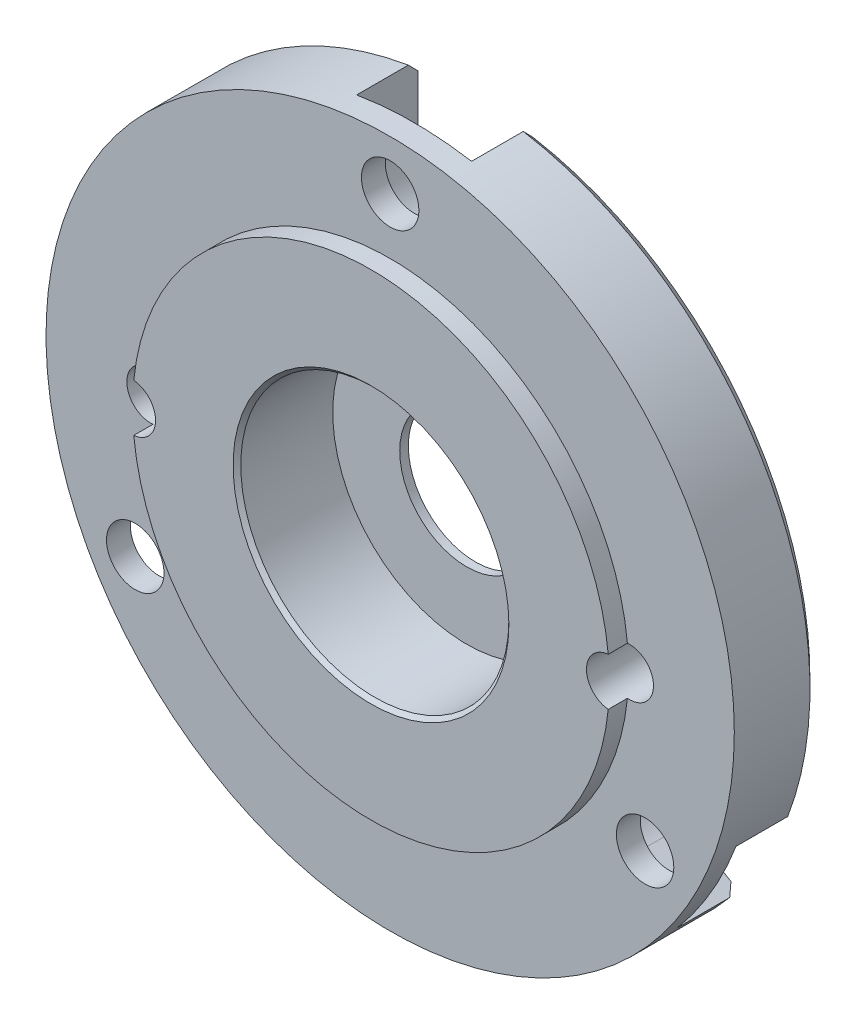
SolidWorks part; units mm, degrees
ref_plane "Plan de face" through (0, 0, 0) normal (0, 0, 1) x (1, 0, 0)
ref_plane "Plan de dessus" through (0, 0, 0) normal (0, 1, 0) x (1, 0, 0)
ref_plane "Plan de droite" through (0, 0, 0) normal (1, 0, 0) x (0, 0, -1)
sketch "Esquisse1" plane through (0, 0, 0) normal (0, 0, 1) x (1, 0, 0)
  circle A0 centre (-74.8422, 51.8721) radius 17.97
extrude "Boss.-Extru.1" add sketch "Esquisse1" along normal blind 4.45
sketch "Esquisse2" plane through (0, 0, 4.45) normal (0, 0, 1) x (1, 0, 0)
  circle A0 centre (-74.8422, 51.8721) radius 12.45
  circle A1 centre (-74.8422, 51.8721) radius 17.97 construction
extrude "Boss.-Extru.2" add sketch "Esquisse2" along normal blind 1
chamfer "Chanfrein1" distance 0.5 angle 45 1 edges at (-56.8722, 51.8721, 0)
sketch "Esquisse5" plane through (0, 0, 0) normal (0, 0, -1) x (-1, 0, 0)
  line L0 (74.8422, 69.8421) -> (74.8422, 32.4297) construction
  line L1 (74.8422, 51.8721) -> (54.6893, 40.2368) construction
  line L2 (56.8722, 51.8721) -> (98.2874, 51.8721) construction
  line L3 (74.8422, 51.8721) -> (95.0822, 40.1865) construction
  circle A0 centre (74.8422, 51.8721) radius 17.97 construction
  circle A1 centre (74.8422, 67.2421) radius 1.5
  circle A2 centre (61.5314, 44.1871) radius 1.5
  circle A3 centre (88.153, 44.1871) radius 1.5
  dimension "D3" = 2.6
  dimension "D4" = 15.37
  dimension "D1" = 30
  dimension "D2" = 30
  dimension "D5" = 15.37
extrude "Enlèv. mat.-Extru.1" cut sketch "Esquisse5" against normal through all
sketch "Esquisse6" plane through (0, 0, 0) normal (0, 0, -1) x (-1, 0, 0)
  circle A0 centre (74.8422, 51.8721) radius 3.5
extrude "Enlèv. mat.-Extru.2" cut sketch "Esquisse6" against normal through all
sketch "Esquisse7" plane through (0, 0, 5.45) normal (0, 0, 1) x (1, 0, 0)
  circle A0 centre (-74.8422, 51.8721) radius 7
extrude "Enlèv. mat.-Extru.3" cut sketch "Esquisse7" against normal blind 5
sketch "Esquisse8" plane through (0, 0, 0) normal (0, 0, -1) x (-1, 0, 0)
  line L0 (71.8422, 70.4119) -> (71.8422, 66.3637)
  line L1 (77.8422, 70.4119) -> (77.8422, 66.3637)
  line L2 (71.8422, 70.4119) -> (77.8422, 70.4119)
  line L3 (60.3796, 39.9252) -> (63.8496, 42.0102)
  line L4 (57.2893, 45.0682) -> (60.7594, 47.1532)
  line L5 (60.3796, 39.9252) -> (57.2893, 45.0682)
  line L6 (92.3713, 45.1334) -> (88.8655, 47.1576)
  line L7 (89.3713, 39.9373) -> (85.8655, 41.9614)
  line L8 (92.3713, 45.1334) -> (89.3713, 39.9373)
  circle A0 centre (74.8422, 67.2421) radius 1.5 construction
  arc A1 (71.8422, 66.3637) -> (77.8422, 66.3637) centre (74.8422, 66.3637) ccw
  arc A2 (63.8496, 42.0102) -> (60.7594, 47.1532) centre (62.3045, 44.5817) ccw
  circle A3 centre (74.8422, 51.8721) radius 17.97 construction
  arc A4 (88.8655, 47.1576) -> (85.8655, 41.9614) centre (87.3655, 44.5595) ccw
  dimension "D1" = 6
  dimension "D2" = 3
  dimension "D3" = 18.55
  dimension "D4" = 18.55
extrude "Enlèv. mat.-Extru.4" cut sketch "Esquisse8" against normal blind 3.2
chamfer "Chanfrein2" distance 0.2 angle 45 1 edges at (-67.8422, 51.8721, 5.45)
sketch "Esquisse9" plane through (0, 0, 0) normal (0, 0, -1) x (-1, 0, 0)
  line L0 (56.8722, 51.8721) -> (94.4675, 51.8721) construction
  line L1 (74.8422, 69.8421) -> (74.8422, 32.3814) construction
  arc A0 (71.8422, 69.5899) -> (58.034, 45.5156) centre (74.8422, 51.8721) ccw construction
  circle A1 centre (62.3422, 51.8721) radius 1.25
  circle A2 centre (87.3422, 51.8721) radius 1.25
  arc A4 (77.8422, 69.5899) -> (71.8422, 69.5899) centre (74.8422, 51.8721) ccw construction
  dimension "D1" = 12.5
  dimension "D2" = 12.5
extrude "Enlèv. mat.-Extru.5" cut sketch "Esquisse9" against normal through all
